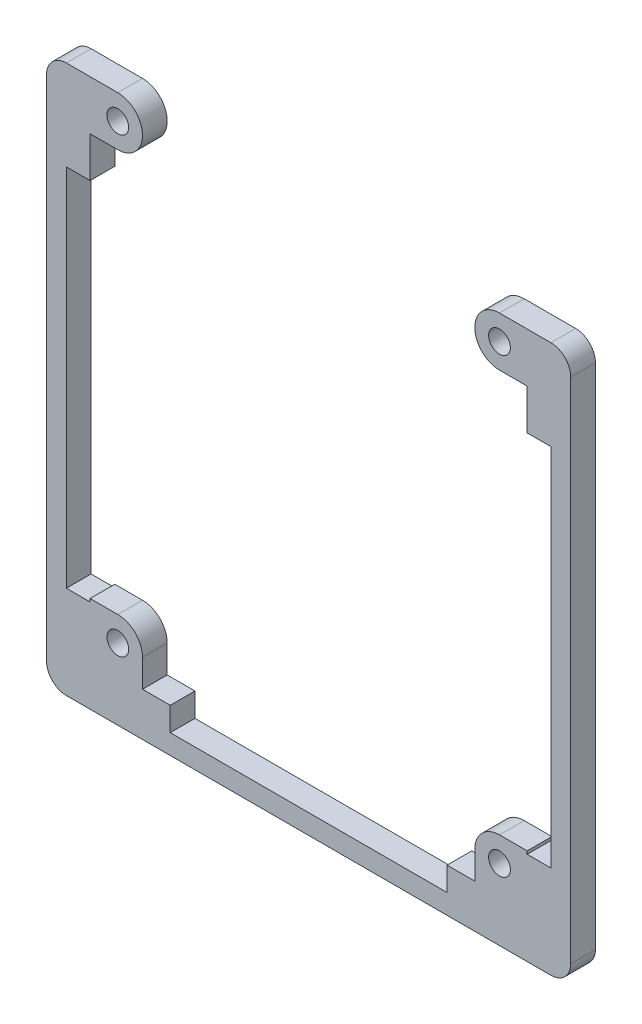
SolidWorks part; units mm, degrees
ref_plane "Front Plane" through (0, 0, 0) normal (0, 0, 1) x (1, 0, 0)
ref_plane "Top Plane" through (0, 0, 0) normal (0, 1, 0) x (1, 0, 0)
ref_plane "Right Plane" through (0, 0, 0) normal (1, 0, 0) x (0, 0, -1)
sketch "Sketch1" plane through (0, 0, 0) normal (0, 0, 1) x (1, 0, 0)
  line L1 (0, 6.35) -> (0, 53.213) construction
  line L2 (3.048, 6.35) -> (3.048, 53.213) construction
  line L3 (3.048, 6.35) -> (0, 6.35) construction
  line L4 (-59.182, 6.35) -> (-56.134, 6.35) construction
  line L7 (-59.182, 53.213) -> (-56.134, 53.213) construction
  line L8 (-45.847, -3.048) -> (-45.847, 0) construction
  line L9 (-10.287, 0) -> (-45.847, 0) construction
  line L10 (-10.287, -3.048) -> (-45.847, -3.048) construction
  line L11 (-10.287, -3.048) -> (-10.287, 0) construction
  line L12 (0, 53.213) -> (3.048, 53.213)
  line L13 (0, 6.35) -> (0, 53.213)
  line L14 (3.048, 6.35) -> (3.048, 53.213)
  line L15 (3.048, 6.35) -> (0, 6.35)
  line L16 (-59.182, 6.35) -> (-56.134, 6.35)
  line L17 (-59.182, 6.35) -> (-59.182, 53.213)
  line L18 (-56.134, 6.35) -> (-56.134, 53.213)
  line L19 (-59.182, 53.213) -> (-56.134, 53.213)
  line L20 (-45.847, -3.048) -> (-45.847, 0)
  line L21 (-10.287, 0) -> (-45.847, 0)
  line L22 (-10.287, -3.048) -> (-45.847, -3.048)
  line L23 (-10.287, -3.048) -> (-10.287, 0)
  line L24 (-28.067, 0) -> (-28.067, 55.1636) construction
  line L25 (-3.556, 61.595) -> (-3.556, 3.556) construction
  line L26 (-52.578, 61.595) -> (-52.578, 3.556) construction
  line L27 (-52.578, 58.42) -> (-56.134, 58.42)
  line L28 (-59.182, 64.77) -> (3.048, 64.77)
  line L29 (-61.722, 62.23) -> (-61.722, -3.048)
  line L30 (-59.182, -5.588) -> (3.048, -5.588)
  line L31 (5.588, 62.23) -> (5.588, -3.048)
  line L33 (-56.134, 58.42) -> (-56.134, 53.213)
  line L34 (-52.578, 6.731) -> (-56.134, 6.731)
  line L35 (-49.403, 3.556) -> (-49.403, 0)
  line L36 (-45.847, 0) -> (-59.182, 0) construction
  line L37 (-49.403, 0) -> (-45.847, 0)
  line L38 (-10.287, 0) -> (-6.731, 0)
  line L39 (3.048, 0) -> (-10.287, 0) construction
  line L40 (-6.731, 0) -> (-6.731, 3.556)
  line L41 (-3.556, 6.731) -> (0, 6.731)
  line L42 (-3.556, 58.42) -> (0, 58.42)
  line L44 (0, 58.42) -> (0, 53.213)
  line L46 (-56.134, 6.731) -> (-56.134, 6.35)
  line L47 (0, 6.35) -> (0, 6.731)
  line L48 (-6.731, 0) -> (-10.287, 0)
  circle A0 centre (-3.556, 3.556) radius 1.397
  circle A1 centre (-3.556, 61.595) radius 1.397
  circle A2 centre (-52.578, 61.595) radius 1.397
  circle A3 centre (-52.578, 3.556) radius 1.397
  circle A4 centre (-52.578, 61.595) radius 3.175
  circle A5 centre (-52.578, 3.556) radius 3.175
  circle A6 centre (-3.556, 61.595) radius 3.175
  circle A7 centre (-3.556, 3.556) radius 3.175
  arc A8 (-61.722, -3.048) -> (-59.182, -5.588) centre (-59.182, -3.048) ccw
  arc A9 (3.048, -5.588) -> (5.588, -3.048) centre (3.048, -3.048) ccw
  arc A10 (3.048, 64.77) -> (5.588, 62.23) centre (3.048, 62.23) cw
  arc A11 (-59.182, 64.77) -> (-61.722, 62.23) centre (-59.182, 62.23) ccw
  dimension "D1" = 2.159
  dimension "D2" = 2.794
  dimension "D3" = 2.159
  dimension "D4" = 55.245
  dimension "D5" = 6.35
  dimension "D9" = 2.54
  dimension "D6" = 2.54
  dimension "D7" = 2.54
  dimension "D8" = 2.54
extrude "Boss-Extrude1" add sketch "Sketch1" along normal blind 3.175
sketch "Sketch2" plane through (0, 0, 3.175) normal (0, 0, 1) x (1, 0, 0)
  line L0 (-49.403, 3.556) -> (-49.403, 61.595)
  line L1 (-52.578, 64.77) -> (-3.556, 64.77)
  line L2 (-39.243, -3.048) -> (-39.243, 6.731)
  line L3 (-10.287, -3.048) -> (-45.847, -3.048) construction
  line L4 (-39.243, 6.731) -> (-49.403, 6.731)
  line L5 (-16.891, 6.731) -> (-16.891, -3.048)
  line L6 (-16.891, 6.731) -> (-3.556, 6.731)
  line L7 (-6.731, 3.556) -> (-6.731, 61.595) construction
  line L8 (-39.243, 6.731) -> (-16.891, 6.731)
  line L9 (3.048, 45.72) -> (-20.32, 45.72)
  line L10 (3.048, 6.35) -> (3.048, 53.213) construction
  line L11 (-20.32, 45.72) -> (-20.32, 42.672)
  line L12 (-20.32, 42.672) -> (3.048, 42.672)
  line L13 (-3.556, 58.42) -> (0, 58.42) construction
  line L14 (0, 58.42) -> (0, 53.213) construction
  line L15 (-52.578, 58.42) -> (-49.403, 58.42)
  line L16 (-52.578, 6.731) -> (-49.403, 6.731)
  arc A0 (-52.578, 58.42) -> (-52.578, 64.77) centre (-52.578, 61.595) ccw construction
  arc A1 (-3.556, 64.77) -> (-3.556, 58.42) centre (-3.556, 61.595) ccw construction
  point P29 (-1.778, 58.42)
  arc M10 (-3.556, 64.77) -> (-3.556, 58.42) centre (-3.556, 61.595) ccw
  line M11 (-3.556, 58.42) -> (0, 58.42)
  line M12 (0, 58.42) -> (0, 53.213)
  line M13 (0, 53.213) -> (3.048, 53.213)
  line M14 (3.048, 53.213) -> (3.048, 6.35)
  line M15 (3.048, 6.35) -> (0, 6.35)
  line M16 (0, 6.35) -> (0, 6.731)
  line M17 (0, 6.731) -> (-3.556, 6.731)
  arc M18 (-3.556, 6.731) -> (-6.731, 3.556) centre (-3.556, 3.556) ccw
  line M19 (-6.731, 3.556) -> (-6.731, 0)
  line M20 (-6.731, 0) -> (-10.287, 0)
  line M21 (-10.287, 0) -> (-10.287, -3.048)
  line M22 (-10.287, -3.048) -> (-45.847, -3.048)
  line M23 (-45.847, -3.048) -> (-45.847, 0)
  line M24 (-45.847, 0) -> (-49.403, 0)
  line M25 (-49.403, 0) -> (-49.403, 3.556)
  arc M26 (-49.403, 3.556) -> (-52.578, 6.731) centre (-52.578, 3.556) ccw
  arc M34 (-52.578, 58.42) -> (-52.578, 64.77) centre (-52.578, 61.595) ccw
  dimension "D1" = 10.16
  dimension "D2" = 10.16
  dimension "D3" = 12.7
  dimension "D4" = 3.048
  dimension "D5" = 20.32
extrude "Boss-Extrude2" [suppressed] add sketch "Sketch2" against normal up to vertex contours L6 L7 L12 L11 L9 L1 L0 L4 L8 M10 M34 | L7 L6 L5 M19 M22 M21 M20 | L2 L4 L0 M25 M24 M23 M22 | L7 L6 L12 M17 M16 M15 M14 | L7 L9 M14 M13 M12 M11 M10 | L7 L6 M18 | L15 L0 M34 | L16 L0 M26
